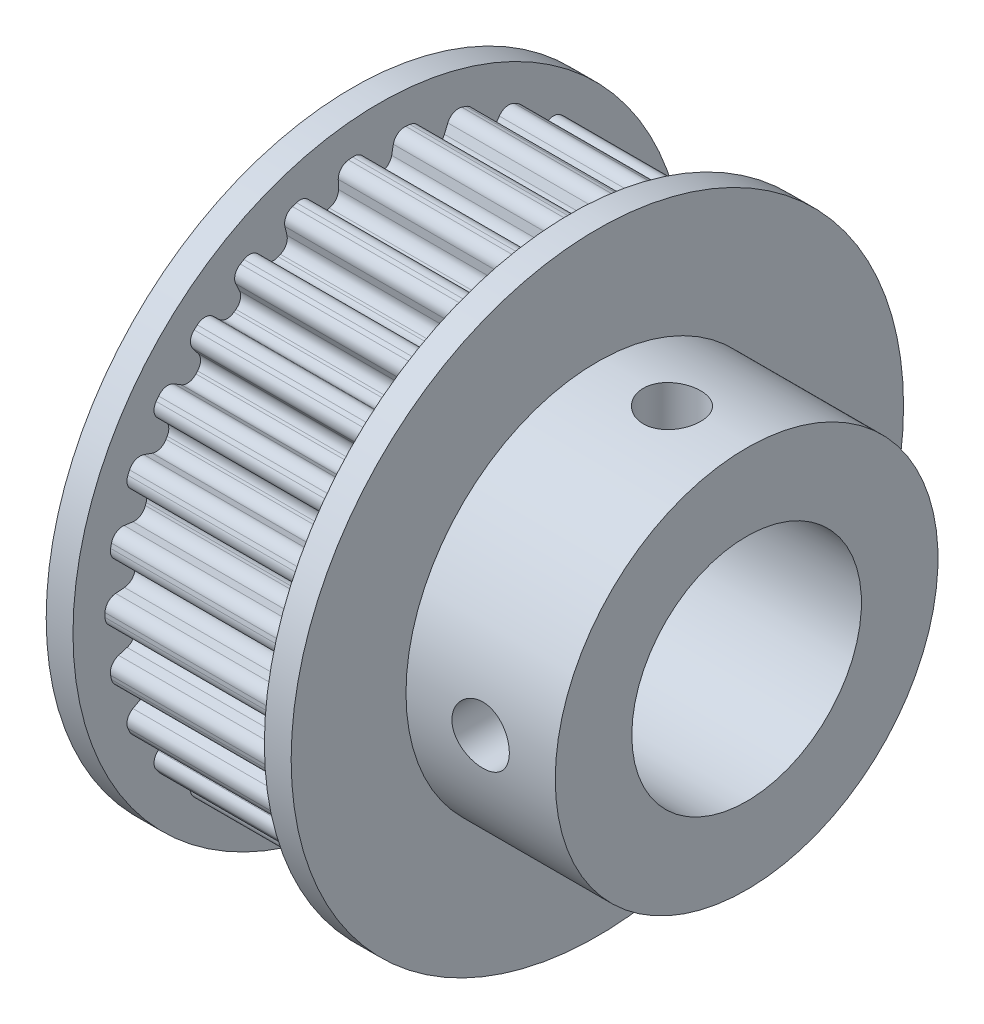
SolidWorks part; units mm, degrees
ref_plane "Ön Düzlem" through (0, 0, 0) normal (0, 0, 1) x (1, 0, 0)
ref_plane "Üst Düzlem" through (0, 0, 0) normal (0, 1, 0) x (1, 0, 0)
ref_plane "Sağ Düzlem" through (0, 0, 0) normal (1, 0, 0) x (0, 0, -1)
sketch "Sketch1" plane through (0, 0, 0) normal (0, 0, 1) x (1, 0, 0)
  line L0 (0, 0) -> (0, 16)
  line L1 (0, 16) -> (1.4, 16)
  line L2 (1.4, 16) -> (1.4, 14.325)
  line L3 (1.4, 14.325) -> (11.4, 14.325)
  line L4 (11.4, 14.325) -> (11.4, 16)
  line L5 (11.4, 16) -> (12.8, 16)
  line L6 (12.8, 16) -> (12.8, 10)
  line L7 (12.8, 10) -> (20.6, 10)
  line L8 (20.6, 10) -> (20.6, 0)
  line L9 (20.6, 0) -> (0, 0)
  line L10 (-2.9355, 0) -> (22.7003, 0) construction
  dimension "D1" = 16
  dimension "D2" = 10
  dimension "D3" = 20.6
  dimension "D4" = 10
  dimension "D5" = 12.8
  dimension "D6" = 14.325
revolve "Revolve1" add sketch "Sketch1" angle 360 about L10
sketch "Sketch2" plane through (0, 0, 0) normal (-1, 0, 0) x (0, 0, 1)
  circle A0 centre (0, 0) radius 6
  dimension "D1" = 12
extrude "Cut-Extrude1" cut sketch "Sketch2" against normal through all
sketch "Sketch4" plane through (0, 0, 0) normal (0, 1, 0) x (1, 0, 0)
  line L0 (12.8, 0) -> (20.6, 0) construction
  line L1 (12.8, -10) -> (12.8, 10) construction
  line L2 (20.6, -10) -> (20.6, 10) construction
  circle A0 centre (16.7, 0) radius 1.5
  dimension "D1" = 3
extrude "Cut-Extrude3" cut sketch "Sketch4" along normal through all
pattern_circular "CirPattern1" count 2 over 90 about axis through (-2.9355, 0, 0) along (-1, 0, 0) of "Cut-Extrude3"
sketch "Sketch3" plane through (1.4, 0, 0) normal (1, 0, 0) x (0, 0, -1)
  line L0 (1.125, 15.825) -> (0.5625, 12.825)
  line L1 (0.5625, 12.825) -> (-0.5625, 12.825)
  line L2 (-0.5625, 12.825) -> (-1.125, 15.825)
  line L3 (-1.125, 15.825) -> (1.125, 15.825)
  circle A0 centre (0, 0) radius 14.325 construction
  point P2 (0, 12.825)
  point P5 (0, 14.325)
  dimension "D1" = 2.25
  dimension "D2" = 1.125
  dimension "D3" = 3
  dimension "D4" = 1.5
extrude "Cut-Extrude2" cut sketch "Sketch3" along normal blind 10
fillet "Fillet1" radius 0.6 4 edges at (6.4, 14.3004, 0.8391) (6.4, 14.3004, -0.8391) (6.4, 12.825, -0.5625) (6.4, 12.825, 0.5625)
pattern_circular "CirPattern2" count 30 over 360 about axis through (0, 0, 0) along (1, 0, 0) of "Cut-Extrude2", "Fillet1"
